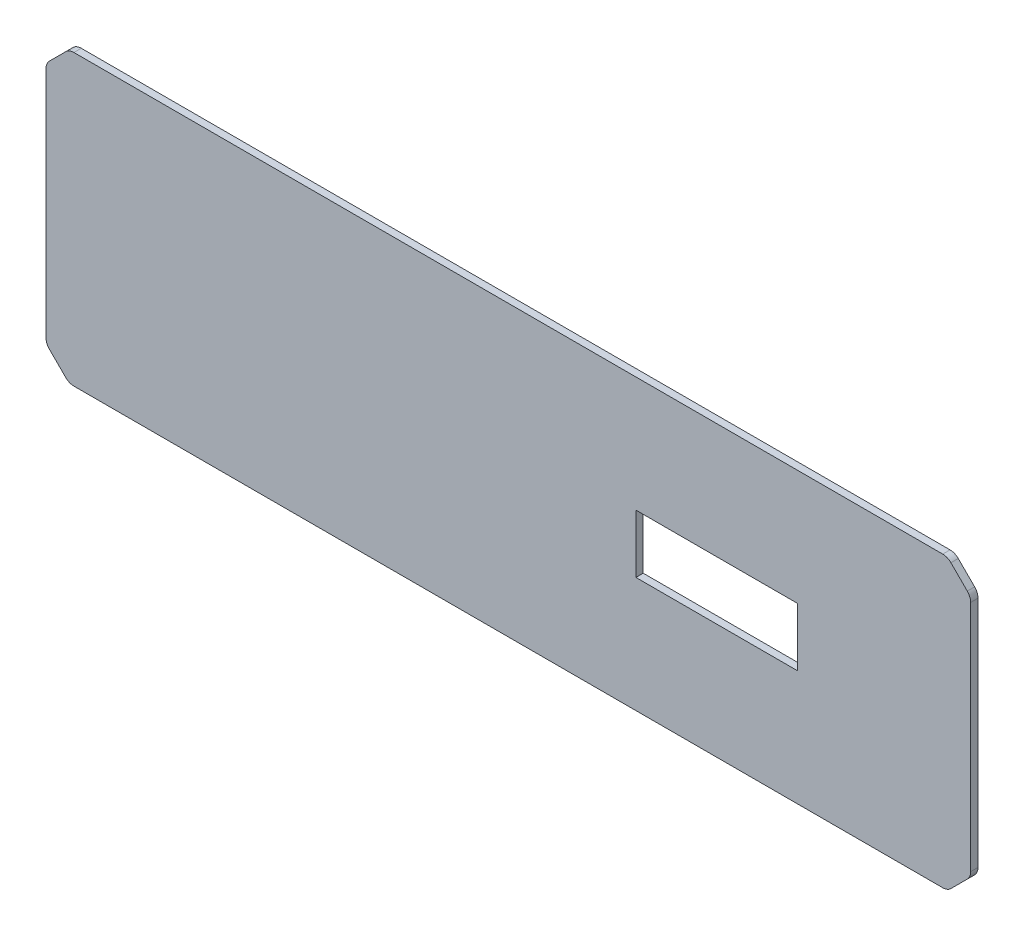
SolidWorks part; units mm, degrees
material "Maple"
ref_plane "Front Plane" through (0, 0, 0) normal (0, 0, 1) x (1, 0, 0)
ref_plane "Top Plane" through (0, 0, 0) normal (0, 1, 0) x (1, 0, 0)
ref_plane "Right Plane" through (0, 0, 0) normal (1, 0, 0) x (0, 0, -1)
sketch "Sketch1" plane through (0, 0, 0) normal (0, 0, 1) x (1, 0, 0)
  line L1 (-200, 62.5) -> (200, 62.5)
  line L2 (-200, 62.5) -> (-200, -62.5)
  line L3 (-200, -62.5) -> (200, -62.5)
  line L4 (200, 62.5) -> (200, -62.5)
  line L5 (-200, 62.5) -> (200, -62.5) construction
  line L6 (-200, -62.5) -> (200, 62.5) construction
  point P0 (0, 0)
  dimension "D1" = 400
  dimension "D2" = 125
extrude "Boss-Extrude1" add sketch "Sketch1" along normal blind 3.175
sketch "Sketch2" plane through (0, 0, 3.175) normal (0, 0, 1) x (1, 0, 0)
  line L0 (200, 0) -> (125, 0) construction
  line L1 (200, -62.5) -> (200, 62.5) construction
  line L2 (125, 0) -> (55.17, 0) construction
  line L4 (125, -12.615) -> (55.17, -12.615)
  line L5 (125, -12.615) -> (125, 12.615)
  line L6 (125, 12.615) -> (55.17, 12.615)
  line L7 (55.17, -12.615) -> (55.17, 12.615)
  line L8 (125, -12.615) -> (55.17, 12.615) construction
  line L9 (125, 12.615) -> (55.17, -12.615) construction
  point P5 (90.085, 0)
  dimension "D1" = 75
  dimension "D2" = 69.83
  dimension "D3" = 25.23
extrude "Cut-Extrude1" cut sketch "Sketch2" against normal blind 3.175
chamfer "Chamfer1" distance 10 angle 45 4 edges at (200, -62.5, 1.5875) (200, 62.5, 1.5875) (-200, 62.5, 1.5875) (-200, -62.5, 1.5875)
fillet "Fillet1" radius 5 8 edges at (-190, 62.5, 1.5875) (-200, 52.5, 1.5875) (-200, -52.5, 1.5875) (-190, -62.5, 1.5875) (190, -62.5, 1.5875) (200, -52.5, 1.5875) (200, 52.5, 1.5875) (190, 62.5, 1.5875)
